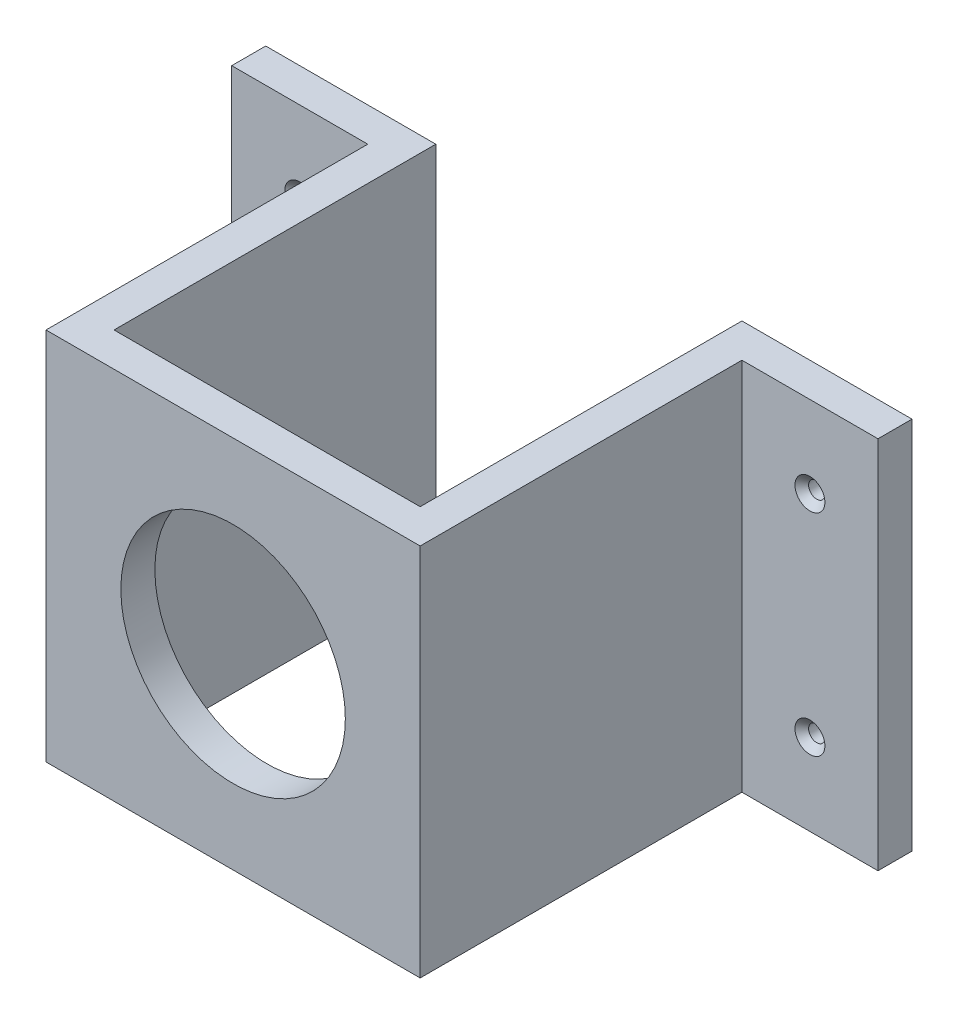
SolidWorks part; units mm, degrees
ref_plane "Ön Düzlem" through (0, 0, 0) normal (0, 0, 1) x (1, 0, 0)
ref_plane "Üst Düzlem" through (0, 0, 0) normal (0, 1, 0) x (1, 0, 0)
ref_plane "Sağ Düzlem" through (0, 0, 0) normal (1, 0, 0) x (0, 0, -1)
sketch "Sketch1" plane through (0, 0, 0) normal (0, 0, 1) x (1, 0, 0)
  line L1 (-27.5, 27.5) -> (27.5, 27.5)
  line L2 (-27.5, 27.5) -> (-27.5, -27.5)
  line L3 (-27.5, -27.5) -> (27.5, -27.5)
  line L4 (27.5, 27.5) -> (27.5, -27.5)
  line L5 (-27.5, 27.5) -> (27.5, -27.5) construction
  line L6 (-27.5, -27.5) -> (27.5, 27.5) construction
  point P0 (0, 0)
  dimension "D1" = 55
  dimension "D2" = 55
extrude "Boss-Extrude1" add sketch "Sketch1" along normal blind 5
sketch "Sketch2" plane through (0, 0, 0) normal (0, 0, -1) x (-1, 0, 0)
  line L0 (27.5, -27.5) -> (-27.5, -27.5) construction
  line L1 (-27.5, 27.5) -> (-22.5, 27.5)
  line L2 (-27.5, 27.5) -> (-27.5, -27.5)
  line L3 (-27.5, -27.5) -> (-22.5, -27.5)
  line L4 (-22.5, 27.5) -> (-22.5, -27.5)
  line L6 (27.5, 27.5) -> (22.5, 27.5)
  line L7 (27.5, 27.5) -> (27.5, -27.5)
  line L8 (27.5, -27.5) -> (22.5, -27.5)
  line L9 (22.5, 27.5) -> (22.5, -27.5)
  dimension "D1" = 5
  dimension "D2" = 5
extrude "Boss-Extrude2" add sketch "Sketch2" along normal blind 47.3
sketch "Sketch3" plane through (0, 0, 5) normal (0, 0, 1) x (1, 0, 0)
  circle A0 centre (0, 0) radius 16.5
  dimension "D1" = 33
extrude "Cut-Extrude1" cut sketch "Sketch3" against normal up to next
sketch "Sketch4" plane through (27.5, 0, 0) normal (1, 0, 0) x (0, 0, -1)
  line L0 (-5, -27.5) -> (47.3, -27.5) construction
  line L1 (47.3, 27.5) -> (42.3, 27.5)
  line L2 (47.3, 27.5) -> (47.3, -27.5)
  line L3 (47.3, -27.5) -> (42.3, -27.5)
  line L4 (42.3, 27.5) -> (42.3, -27.5)
  dimension "D1" = 5
extrude "Boss-Extrude3" add sketch "Sketch4" along normal blind 20
sketch "Sketch5" plane through (-27.5, 0, 0) normal (-1, 0, 0) x (0, 0, 1)
  line L0 (5, -27.5) -> (-47.3, -27.5) construction
  line L1 (-47.3, 27.5) -> (-42.3, 27.5)
  line L2 (-47.3, 27.5) -> (-47.3, -27.5)
  line L3 (-47.3, -27.5) -> (-42.3, -27.5)
  line L4 (-42.3, 27.5) -> (-42.3, -27.5)
  dimension "D1" = 5
extrude "Boss-Extrude4" add sketch "Sketch5" along normal blind 20
hole_wizard "CSK for M2 Flat Head Machine Screw1" positions "Sketch9" profile "Sketch8" countersink size "M2" standard "ANSI Metric" end condition through all
sketch "Sketch9" plane through (0, 0, -42.3) normal (0, 0, 1) x (1, 0, 0)
  line L1 (-47.5, -27.5) -> (-47.5, 27.5) construction
  line L2 (-47.5, 27.5) -> (-27.5, 27.5) construction
  line L3 (-47.5, -27.5) -> (-27.5, -27.5) construction
  line L4 (47.5, 27.5) -> (27.5, 27.5) construction
  line L5 (47.5, -27.5) -> (27.5, -27.5) construction
  line L6 (47.5, 27.5) -> (47.5, -27.5) construction
  point P0 (-37.5, 15.5)
  point P2 (-37.5, -15.5)
  point P4 (37.5, 15.5)
  point P6 (37.5, -15.5)
  dimension "D1" = 10
  dimension "D2" = 10
  dimension "D3" = 12
  dimension "D4" = 12
  dimension "D5" = 12
  dimension "D6" = 12
  dimension "D7" = 10
  dimension "D8" = 10
sketch "Sketch8" plane through (-37.5, 15.5, -42.3) normal (1, 0, 0) x (0, -1, 0)
  line L0 (0, 0) -> (0, 5)
  line L1 (0, 5) -> (1.2, 5)
  line L2 (1.2, 5) -> (1.2, 1)
  line L3 (1.2, 1) -> (2.2, 0)
  line L5 (2.2, 0) -> (0, 0)
  line L6 (-1.2, 1) -> (-2.2, 0) construction
  line L11 (0, -6.35) -> (0, 107.95) construction
  dimension "Thru Hole Dia." = 2.4
  dimension "Thru Hole Depth" = 5
  dimension "Near C'Sink Dia." = 4.4
  dimension "Near C'Sink Angle" = 90
